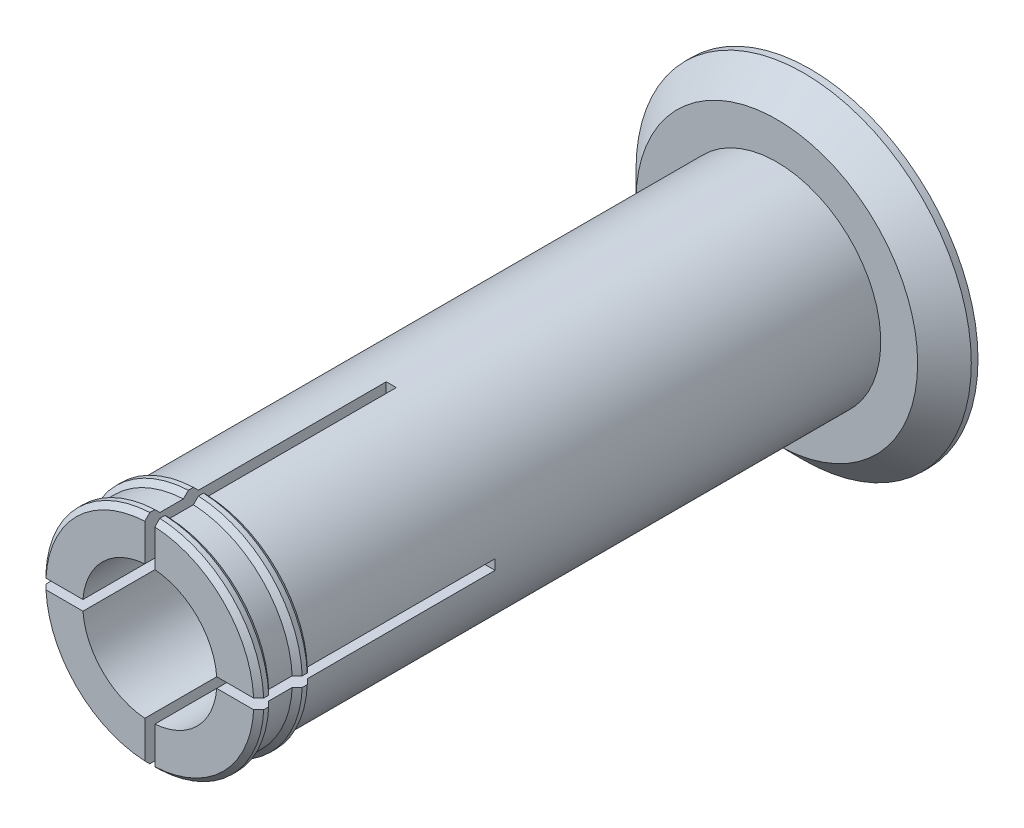
SolidWorks part; units mm, degrees
ref_plane "Front" through (0, 0, 0) normal (0, 0, 1) x (1, 0, 0)
ref_plane "Top" through (0, 0, 0) normal (0, 1, 0) x (1, 0, 0)
ref_plane "Right" through (0, 0, 0) normal (1, 0, 0) x (0, 0, -1)
sketch "Axle base sketch" plane through (0, 0, 0) normal (0, 0, 1) x (1, 0, 0)
  circle A0 centre (0, 0) radius 15.5
  dimension "D1" = 31
extrude "Axle" add sketch "Axle base sketch" along normal blind 93.5
sketch "Guard base" plane through (0, 0, 0) normal (0, 0, -1) x (-1, 0, 0)
  circle A0 centre (0, 0) radius 25
  dimension "D1" = 50
extrude "Guard" add sketch "Guard base" along normal blind 5
sketch "Inner axle hole base" plane through (0, 0, 93.5) normal (0, 0, 1) x (1, 0, 0)
  circle A0 centre (0, 0) radius 10
  dimension "D1" = 20
extrude "Inner axle hole" cut sketch "Inner axle hole base" against normal through all
sketch "Mate ring base" plane through (0, 0, 0) normal (0, 1, 0) x (1, 0, 0)
  line L0 (15.5, -93.5) -> (16.25, -92.75)
  line L1 (16.25, -92.75) -> (16.25, -92)
  line L2 (16.25, -92) -> (15.5, -91.25)
  line L3 (16.25, -92.75) -> (16.25, -93.5) construction
  line L4 (16.25, -93.5) -> (15.5, -93.5) construction
  line L5 (15.5, -91.25) -> (15.5, -93.5)
  line L6 (15.5, -93.5) -> (15.5, 0) construction
  line L8 (15.5, -87.75) -> (16.25, -87)
  line L9 (16.25, -87) -> (16.25, -86.25)
  line L10 (16.25, -86.25) -> (15.5, -85.5)
  line L11 (15.5, -85.5) -> (15.5, -87.75)
  dimension "D1" = 0.75
  dimension "D2" = 0.75
  dimension "D3" = 5
  dimension "D4" = 0.75
ref_axis "Center Z" through (0, 0, 0) along (0, 0, -1)
revolve "Mate rings" add sketch "Mate ring base" angle 360 about axis through (0, 0, 0) along (0, 0, -1)
sketch "Bend room base" plane through (0, 0, 93.5) normal (0, 0, 1) x (1, 0, 0)
  line L0 (0.75, -25) -> (0.75, 25)
  line L1 (0.75, 25) -> (-0.75, 25)
  line L2 (-0.75, 25) -> (-0.75, -25)
  line L3 (-0.75, -25) -> (0.75, -25)
  dimension "D1" = 0.75
  dimension "D2" = 0.75
  dimension "D3" = 25
  dimension "D4" = 25
extrude "Bend room 1" cut sketch "Bend room base" against normal blind 36
pattern_circular "Bend room 2" count 2 every 90 about axis through (0, 0, 0) along (0, 0, -1) of "Bend room 1"
chamfer "Chamfer1" distance 4 angle 45 1 edges at (-25, 0, 0)
equation "\"32_92_spool_inner_diameter\"=32"
equation "\"D1@Axle base sketch\"=\"32_92_spool_inner_diameter\"- \"spool_inner_diameter_room\""
equation "\"spool_inner_diameter_room\"=1"
equation "\"32_92_spool_thickness\"=92"
equation "\"D1@Axle\"=\"32_92_spool_thickness\"+\"guard_thickness\"+\"removal_room\"*2 + \"32_92_extra_spool_thickness\""
equation "\"32_92_guard_diameter\"=50"
equation "\"D1@Guard base\"=\"32_92_guard_diameter\""
equation "\"guard_thickness\"=5"
equation "\"D1@Guard\"=\"guard_thickness\""
equation "\"large_inner_axle_diameter\"=20"
equation "\"D1@Inner axle hole base\"=\"large_inner_axle_diameter\""
equation "\"mate_room\"= 0.25"
equation "\"removal_room\"= 0.75"
equation "\"small_inner_axle_diameter\"=17"
equation "\"53_55_spool_inner_diameter\"=53"
equation "\"53_55_spool_thickness\"=55"
equation "\"53_55_guard_diameter\"=75"
equation "\"53_55_coupling_tooth_height\"=27"
equation "\"53_55_coupling_tooth_thickness_total\"=8"
equation "\"53_55_coupling_tooth_protrusion\"=1.5"
equation "\"53_55_coupling_tooth_head_height\"=7.5"
equation "\"53_55_coupling_tooth_depth\"=10"
equation "\"53_55_coupling_tooth_base_thickness\"=9.5"
equation "\"D1@Mate ring base\"=\"removal_room\""
equation "\"D2@Mate ring base\"=\"removal_room\""
equation "\"D3@Mate ring base\"=\"guard_thickness\""
equation "\"D4@Mate ring base\"=\"removal_room\""
equation "\"D1@Bend room base\" = \"removal_room\""
equation "\"D2@Bend room base\"=\"removal_room\""
equation "\"D3@Bend room base\"=\"32_92_guard_diameter\"/2"
equation "\"D4@Bend room base\"=\"32_92_guard_diameter\"/2"
equation "\"bend_room_length_multiplier\"=3"
equation "\"D1@Bend room 1\"=\"bend_room_length_multiplier\"*(\"32_92_spool_inner_diameter\"-\"large_inner_axle_diameter\")"
equation "\"D1@Chamfer1\"=\"guard_thickness\"-1"
equation "\"32_92_extra_spool_thickness\"=-5"
